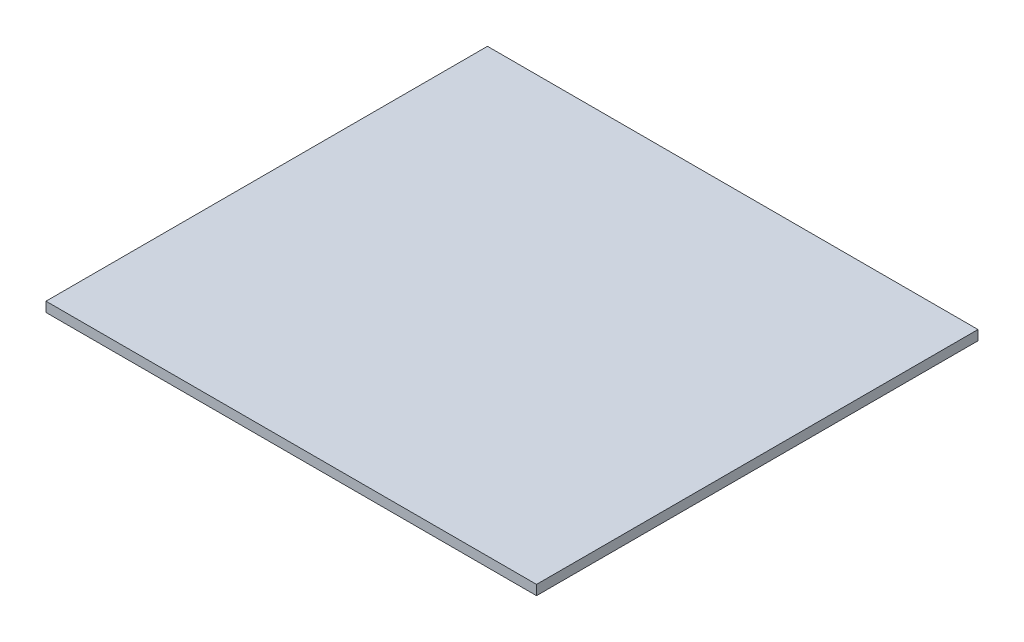
SolidWorks part; units mm, degrees
ref_plane "Front Plane" through (0, 0, 0) normal (0, 0, 1) x (1, 0, 0)
ref_plane "Top Plane" through (0, 0, 0) normal (0, 1, 0) x (1, 0, 0)
ref_plane "Right Plane" through (0, 0, 0) normal (1, 0, 0) x (0, 0, -1)
sketch "Sketch1" plane through (0, 0, 0) normal (0, 1, 0) x (1, 0, 0)
  line L1 (0, 0) -> (254, 0)
  line L2 (0, 0) -> (0, 228.6)
  line L3 (0, 228.6) -> (254, 228.6)
  line L4 (254, 0) -> (254, 228.6)
  dimension "D1" = 228.6
  dimension "D2" = 254
extrude "Boss-Extrude1" add sketch "Sketch1" along normal blind 5.08
equation "\"MDF\"= 0.2in"
equation "\"Foamcore\"= 0.2in"
equation "\"D1@Boss-Extrude1\"=\"MDF\""
equation "\"BaseWidth\"= 9in"
equation "\"BaseLength\"= 9in"
